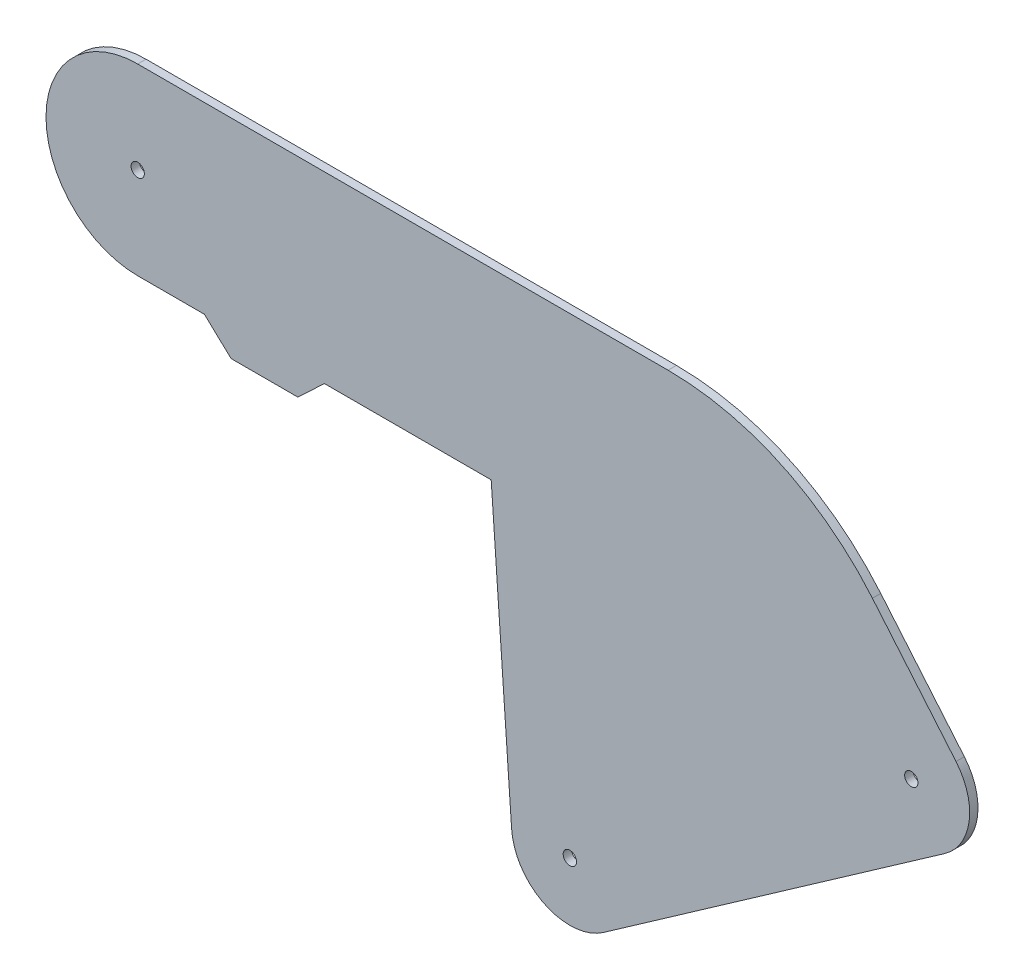
SolidWorks part; units mm, degrees
material "ABS PC"
ref_plane "Front Plane" through (0, 0, 0) normal (0, 0, 1) x (1, 0, 0)
ref_plane "Top Plane" through (0, 0, 0) normal (0, 1, 0) x (1, 0, 0)
ref_plane "Right Plane" through (0, 0, 0) normal (1, 0, 0) x (0, 0, -1)
sketch "Sketch1" plane through (0, 0, 0) normal (0, 0, 1) x (1, 0, 0)
  line L0 (0, 0) -> (0, 215.9) construction
  line L1 (133.35, 0) -> (133.35, 171.45) construction
  line L2 (0.0421, 0) -> (133.3921, 0) construction
  line L3 (50.8, 0) -> (50.8, 123.825) construction
  line L4 (508, 0) -> (508, 50000) construction
  line L11 (133.35, 171.45) -> (0, 171.45) construction
  line L20 (508, 457.2) -> (482.6, 457.2) construction
  line L22 (-203.2, 0) -> (-203.2, 53.1862) construction
  line L31 (-203.2, 520.7) -> (50.8, 520.7) construction
  line L48 (294.6125, 162.3041) -> (164.5721, 71.2488) construction
  line L52 (0, 180.975) -> (134.62, 180.975) construction
  line L53 (134.62, 180.975) -> (142.4012, 69.6985)
  line L62 (177.3198, 53.0432) -> (307.3602, 144.0984)
  line L66 (25.4, 180.975) -> (35.56, 171.45)
  line L67 (35.56, 171.45) -> (60.96, 171.45)
  line L68 (60.96, 171.45) -> (71.12, 180.975)
  line L69 (71.12, 180.975) -> (134.62, 180.975)
  line L70 (0, 250.825) -> (201.9704, 250.825)
  line L71 (279.8005, 214.5322) -> (311.6378, 176.59)
  line L72 (0, 180.975) -> (25.4, 180.975)
  circle A11 centre (508, 75.057) radius 75.057 construction
  arc A19 (0, 250.825) -> (0, 180.975) centre (0, 215.9) ccw
  circle A23 centre (294.6125, 162.3041) radius 2.54
  circle A24 centre (164.5721, 71.2488) radius 2.54
  circle A25 centre (0, 215.9) radius 2.54
  arc A28 (201.9704, 250.825) -> (279.8005, 214.5322) centre (201.9704, 149.225) cw
  circle A29 centre (294.6125, 162.3041) radius 12.7 construction
  arc A32 (311.6378, 176.59) -> (307.3602, 144.0984) centre (294.6125, 162.3041) cw
  circle A33 centre (164.5721, 71.2488) radius 12.7 construction
  arc A34 (142.4012, 69.6985) -> (177.3198, 53.0432) centre (164.5721, 71.2488) ccw
  point P2 (-43.666, 416.1625)
  point P10 (-144.3546, 361.4114)
  point P17 (-177.8, 889)
  point P18 (279.8039, 215.9)
  point P24 (-165.161, 337.2822)
  point P27 (177.3198, 53.0432)
  point P32 (202.1745, 249.6232)
  point P38 (201.9704, 250.825)
  point P42 (134.62, 180.975)
  dimension "D4" = 304.8
  dimension "D9" = 49.53
  dimension "D10" = 134.62
  dimension "D11" = 158.75
  dimension "D12" = 59
  dimension "D13" = 150.114
  dimension "D14" = 94
  dimension "D21" = 25.4
  dimension "D3" = 171.45
  dimension "D6" = 130
  dimension "D15" = 25.4
  dimension "D23" = 25.4
  dimension "D8" = 69.85
  dimension "D28" = 5.08
  dimension "D29" = 9.525
  dimension "D30" = 101.6
  dimension "D24" = 22.225
  dimension "D26" = 25.4
  dimension "D1" = 82.55
  dimension "D2" = 215.9
  dimension "D5" = 50.8
  dimension "D7" = 457.2
  dimension "D17" = 457.2
  dimension "D18" = 177.8
  dimension "D19" = 889
  dimension "D20" = 25.4
  dimension "4.5" = 203.2
  dimension "D27" = 63.5
extrude "Boss-Extrude1" add sketch "Sketch1" along normal blind 3.175
